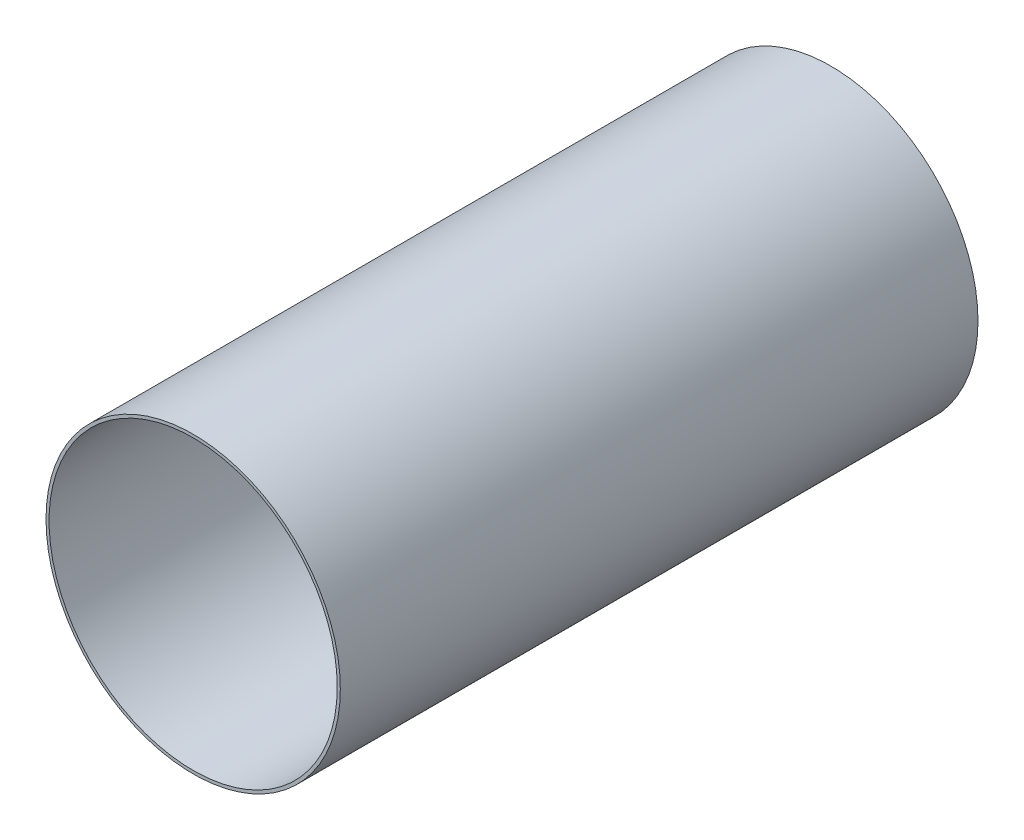
SolidWorks part; units mm, degrees
material "6061-T6 (SS)"
ref_plane "Front Plane" through (0, 0, 0) normal (0, 0, 1) x (1, 0, 0)
ref_plane "Top Plane" through (0, 0, 0) normal (0, 1, 0) x (1, 0, 0)
ref_plane "Right Plane" through (0, 0, 0) normal (1, 0, 0) x (0, 0, -1)
sketch "Sketch1" plane through (0, 0, 0) normal (0, 0, 1) x (1, 0, 0)
  circle A0 centre (0, 0) radius 152.4
  dimension "D1" = 304.8
extrude "Boss-Extrude1" add sketch "Sketch1" along normal blind 660.4 contours A0
sketch "Sketch2" plane through (0, 0, 660.4) normal (0, 0, 1) x (1, 0, 0)
  circle A0 centre (0, 0) radius 149.225
  dimension "D1" = 298.45
extrude "Cut-Extrude1" cut sketch "Sketch2" against normal blind 660.4 contours A0
sketch "Sketch3" plane through (0, 0, 0) normal (0, 1, 0) x (1, 0, 0)
  line L0 (0, 0) -> (0, -25.4) construction
  circle A0 centre (0, -25.4) radius 3.175
  dimension "D1" = 6.35
extrude "Cut-Extrude2" [suppressed] cut sketch "Sketch3" along normal blind 190.5 contours A0
pattern_circular "CirPattern3" [suppressed] count 8 over 360
sketch "Sketch4" plane through (0, 0, 0) normal (0, 1, 0) x (1, 0, 0)
  line L0 (0, -635) -> (0, 0)
  line L1 (-152.4, -660.4) -> (152.4, -660.4) construction
  line L2 (0, -660.4) -> (0, -635) construction
  circle A0 centre (0, -635) radius 3.175
  dimension "D1" = 6.35
  dimension "D2" = 635
extrude "Cut-Extrude4" [suppressed] cut sketch "Sketch4" against normal blind 270.764 contours A0
pattern_circular "CirPattern5" [suppressed] count 8 over 360
equation "\"Rocket Diameter\"= 12in"
equation "\"D1@Sketch1\"=\"Rocket Diameter\""
equation "\"Airframe Thickness\"= 0.125in"
equation "\"Length\"= 26in"
equation "\"D1@Boss-Extrude1\"=\"Length\""
equation "\"D1@Cut-Extrude1\"=\"Length\""
equation "\"Bolt Diameter\"= 0.25in"
equation "\"D1@Sketch3\"=\"Bolt Diameter\""
equation "\"D1@Sketch2\"= \"Rocket Diameter\"-\"Airframe Thickness\"*2"
equation "\"D1@Sketch4\"=\"Bolt Diameter\""
equation "\"D2@Sketch4\"=\"Length\"-1in"
